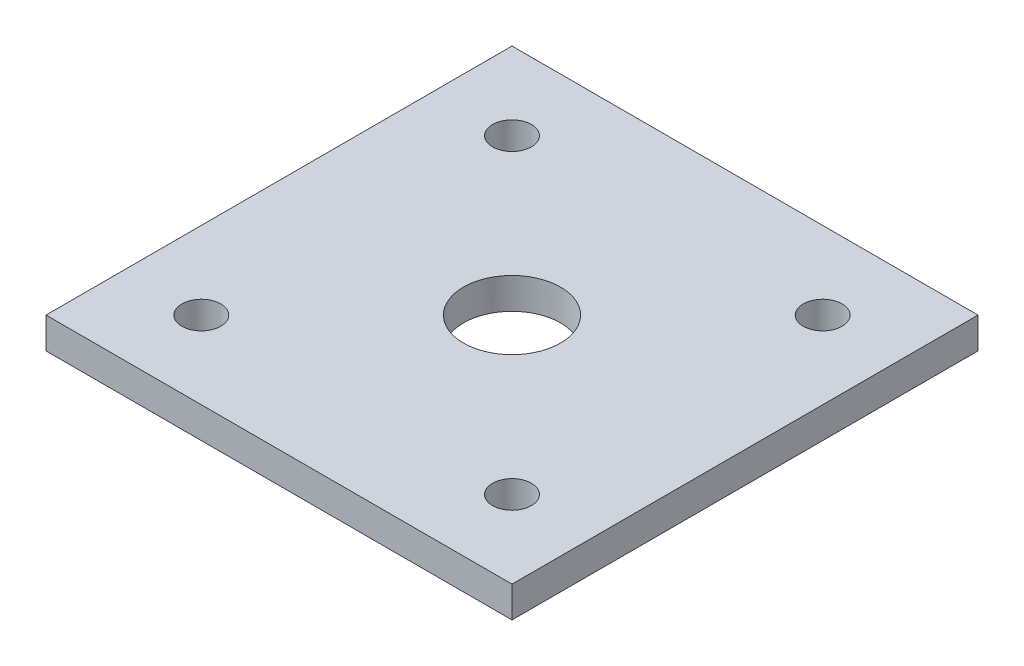
SolidWorks part; units mm, degrees
ref_plane "Front Plane" through (0, 0, 0) normal (0, 0, 1) x (1, 0, 0)
ref_plane "Top Plane" through (0, 0, 0) normal (0, 1, 0) x (1, 0, 0)
ref_plane "Right Plane" through (0, 0, 0) normal (1, 0, 0) x (0, 0, -1)
sketch "Sketch1" plane through (0, 0, 0) normal (0, 1, 0) x (1, 0, 0)
  line L1 (60, -60) -> (-60, -60)
  line L2 (60, -60) -> (60, 60)
  line L3 (60, 60) -> (-60, 60)
  line L4 (-60, -60) -> (-60, 60)
  line L5 (60, -60) -> (-60, 60) construction
  line L6 (60, 60) -> (-60, -60) construction
  point P0 (0, 0)
  dimension "D1" = 120
  dimension "D2" = 120
extrude "Boss-Extrude1" add sketch "Sketch1" along normal blind 8 contours L2 L1 L4 L3
sketch "Sketch2" plane through (0, 8, 0) normal (0, 1, 0) x (1, 0, 0)
  circle A0 centre (0, 0) radius 12.5
  dimension "D1" = 25
extrude "Cut-Extrude1" cut sketch "Sketch2" against normal blind 10
sketch "Sketch3" plane through (0, 0, 0) normal (0, -1, 0) x (1, 0, 0)
  line L2 (-60, -60) -> (-60, 60) construction
  line L3 (60, -60) -> (-60, -60) construction
  circle A2 centre (-40, -40) radius 5
  dimension "D1" = 10
  dimension "D3" = 20
  dimension "D2" = 20
extrude "Cut-Extrude2" cut sketch "Sketch3" against normal blind 10
pattern_linear "LPattern1" count 2 spacing 80 along (0, 0, 1) count 2 spacing 80 along (1, 0, 0) of "Cut-Extrude2"
